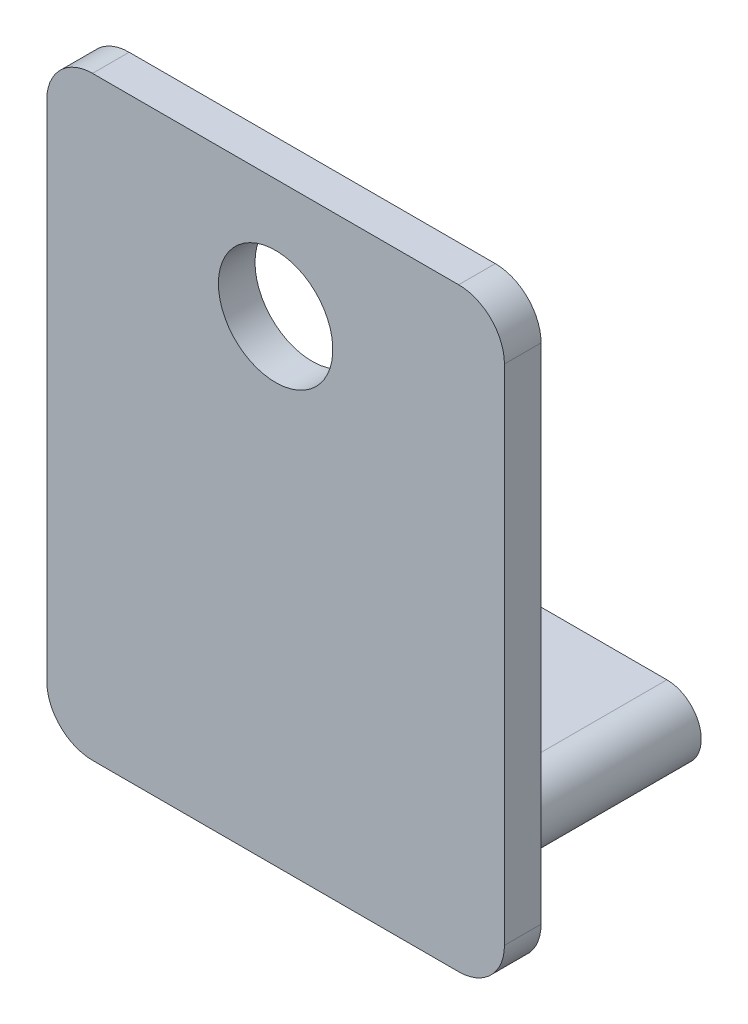
SolidWorks part; units mm, degrees
material "ABS"
ref_plane "前视基准面" through (0, 0, 0) normal (0, 0, 1) x (1, 0, 0)
ref_plane "上视基准面" through (0, 0, 0) normal (0, 1, 0) x (1, 0, 0)
ref_plane "右视基准面" through (0, 0, 0) normal (1, 0, 0) x (0, 0, -1)
sketch "草图1" plane through (0, 0, 0) normal (0, 0, 1) x (1, 0, 0)
  line L1 (-4.7674, 6.3514) -> (3.2326, 6.3514)
  line L2 (-5.7674, 5.3514) -> (-5.7674, -5.6486)
  line L3 (-4.7674, -6.6486) -> (3.2326, -6.6486)
  line L4 (4.2326, 5.3514) -> (4.2326, -5.6486)
  arc A0 (3.2326, 6.3514) -> (4.2326, 5.3514) centre (3.2326, 5.3514) cw
  arc A1 (3.2326, -6.6486) -> (4.2326, -5.6486) centre (3.2326, -5.6486) ccw
  arc A2 (-5.7674, -5.6486) -> (-4.7674, -6.6486) centre (-4.7674, -5.6486) ccw
  arc A3 (-4.7674, 6.3514) -> (-5.7674, 5.3514) centre (-4.7674, 5.3514) ccw
  point P6 (4.2326, 6.3514)
  point P9 (4.2326, -6.6486)
  point P14 (-5.7674, 6.3514)
  dimension "D3" = 1
  dimension "D1" = 13
  dimension "D2" = 10
extrude "凸台-拉伸1" add sketch "草图1" along normal blind 0.8
sketch "草图2" plane through (0, 0, 0) normal (0, 0, -1) x (-1, 0, 0)
  line L0 (-3.2326, 6.3514) -> (4.7674, 6.3514) construction
  line L1 (5.7674, 5.3514) -> (5.7674, -5.6486) construction
  circle A0 centre (0.7674, 3.7514) radius 1.25
  dimension "D1" = 2.5
  dimension "D2" = 2.6
  dimension "D3" = 5
extrude "切除-拉伸1" cut sketch "草图2" against normal up to next
sketch "草图3" plane through (0, 0, 0) normal (0, 0, -1) x (-1, 0, 0)
  line L0 (-1.9826, -5.3986) -> (3.5174, -5.3986) construction
  line L1 (-1.9826, -4.6486) -> (3.5174, -4.6486)
  line L2 (-1.9826, -6.1486) -> (3.5174, -6.1486)
  line L3 (4.7674, -6.6486) -> (-3.2326, -6.6486) construction
  line L4 (5.7674, 5.3514) -> (5.7674, -5.6486) construction
  arc A0 (-1.9826, -4.6486) -> (-1.9826, -6.1486) centre (-1.9826, -5.3986) ccw
  arc A1 (3.5174, -6.1486) -> (3.5174, -4.6486) centre (3.5174, -5.3986) ccw
  point P2 (0.7674, -5.3986)
  point P9 (-2.7326, -5.3986)
  point P10 (4.2674, -5.3986)
  dimension "D1" = 1.5
  dimension "D2" = 2
  dimension "D3" = 7
  dimension "D4" = 5
extrude "凸台-拉伸2" add sketch "草图3" along normal blind 5
